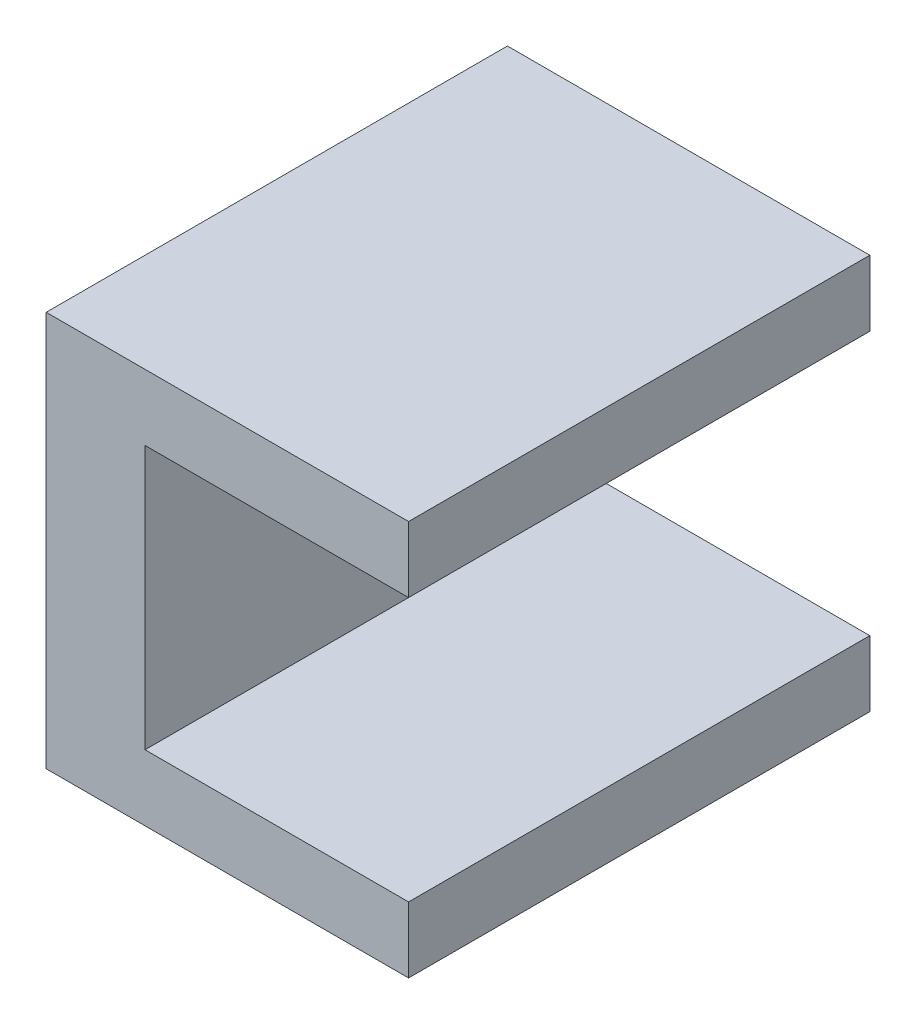
SolidWorks part; units mm, degrees
ref_plane "Front Plane" through (0, 0, 0) normal (0, 0, 1) x (1, 0, 0)
ref_plane "Top Plane" through (0, 0, 0) normal (0, 1, 0) x (1, 0, 0)
ref_plane "Right Plane" through (0, 0, 0) normal (1, 0, 0) x (0, 0, -1)
sketch "Sketch1" plane through (0, 0, 0) normal (0, 1, 0) x (1, 0, 0)
  line L1 (-2.3812, -11.1125) -> (2.3813, -11.1125)
  line L2 (-2.3812, -11.1125) -> (-2.3812, 11.1125)
  line L3 (-2.3812, 11.1125) -> (2.3813, 11.1125)
  line L4 (2.3813, -11.1125) -> (2.3813, 11.1125)
  line L5 (-2.3812, -11.1125) -> (2.3813, 11.1125) construction
  line L6 (-2.3812, 11.1125) -> (2.3813, -11.1125) construction
  point P0 (0, 0)
  dimension "D1" = 4.7625
  dimension "D2" = 22.225
extrude "Boss-Extrude1" add sketch "Sketch1" along normal blind 3.175
sketch "Sketch2" plane through (0, 3.175, 0) normal (0, 1, 0) x (1, 0, 0)
  line L9 (2.3813, 11.1125) -> (-2.3812, 11.1125) construction
  line L10 (2.3813, -11.1125) -> (2.3813, 11.1125) construction
  line L11 (2.3813, 11.1125) -> (-2.3812, 11.1125)
  line L12 (2.3813, 11.1125) -> (2.3812, -11.1125)
  line L13 (2.3812, -11.1125) -> (-2.3812, -11.1125)
  line L14 (-2.3812, 11.1125) -> (-2.3812, -11.1125)
  line L15 (-2.3812, -11.1125) -> (2.3813, -11.1125) construction
  line L16 (-2.3812, 11.1125) -> (-2.3812, -11.1125) construction
extrude "Boss-Extrude2" add sketch "Sketch2" along normal blind 15.875
sketch "Sketch3" plane through (-2.3812, 0, 0) normal (-1, 0, 0) x (0, 0, 1)
  line L0 (0, 19.05) -> (0, 0) construction
  line L3 (-11.1125, 19.05) -> (11.1125, 19.05) construction
  line L4 (-11.1125, 0) -> (11.1125, 0) construction
  circle A0 centre (3.175, 11.1125) radius 1
  circle A1 centre (-3.175, 11.1125) radius 1
  point P4 (0, 0)
  point P7 (0, 0)
  point P8 (0, 0)
  point P11 (0, 0)
  point P12 (0, 0)
  point P13 (6.7589, 19.05)
  point P16 (0, 0)
  point P17 (0, 0)
  dimension "D2" = 2
  dimension "D1" = 6.35
  dimension "D3" = 11.1125
  dimension "D4" = 7.9375
extrude "Cut-Extrude1" cut sketch "Sketch3" against normal through all contours A1 | A0
sketch "Sketch5" plane through (2.3813, 0, 0) normal (1, 0, 0) x (0, 0, -1)
  line L0 (11.1125, 19.05) -> (11.1125, 0) construction
  line L1 (-11.1125, 19.05) -> (11.1125, 19.05)
  line L2 (-11.1125, 19.05) -> (-11.1125, 15.875)
  line L3 (-11.1125, 15.875) -> (11.1125, 15.875)
  line L4 (11.1125, 19.05) -> (11.1125, 15.875)
  line L5 (-11.1125, 19.05) -> (-11.1125, 0) construction
  line L6 (11.1125, 0) -> (-11.1125, 0)
  line L7 (11.1125, 0) -> (11.1125, 3.175)
  line L8 (11.1125, 3.175) -> (-11.1125, 3.175)
  line L9 (-11.1125, 0) -> (-11.1125, 3.175)
  dimension "D1" = 3.175
extrude "Boss-Extrude3" add sketch "Sketch5" along normal blind 12.7
